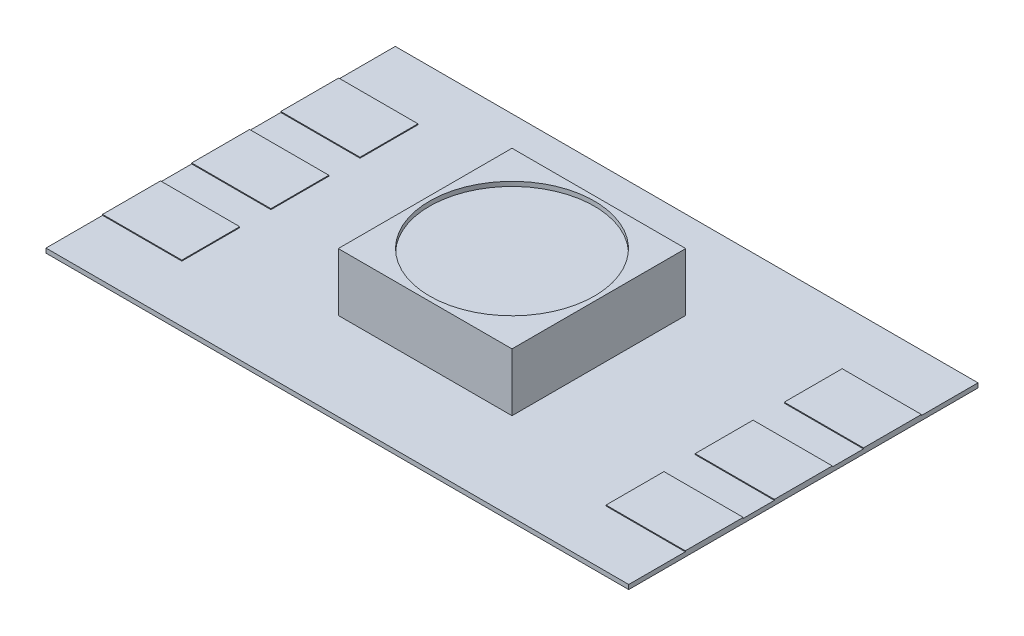
SolidWorks part; units mm, degrees
ref_plane "Front Plane" through (0, 0, 0) normal (0, 0, 1) x (1, 0, 0)
ref_plane "Top Plane" through (0, 0, 0) normal (0, 1, 0) x (1, 0, 0)
ref_plane "Right Plane" through (0, 0, 0) normal (1, 0, 0) x (0, 0, -1)
sketch "Sketch1" plane through (0, 0, 0) normal (0, 1, 0) x (1, 0, 0)
  line L0 (-8.3058, 4.9784) -> (8.3058, -4.9784) construction
  line L1 (-8.3058, 4.9784) -> (8.3058, 4.9784)
  line L2 (-8.3058, 4.9784) -> (-8.3058, -4.9784)
  line L3 (-8.3058, -4.9784) -> (8.3058, -4.9784)
  line L4 (8.3058, 4.9784) -> (8.3058, -4.9784)
  dimension "D1" = 9.9568
  dimension "D2" = 16.6116
extrude "Boss-Extrude1" add sketch "Sketch1" along normal blind 0.127
sketch "Sketch3" plane through (0, 0.127, 0) normal (0, 1, 0) x (1, 0, 0)
  line L0 (-8.3058, 4.9784) -> (8.3058, -4.9784) construction
  line L1 (-2.4765, 2.4765) -> (2.4765, -2.4765) construction
  line L2 (-2.4765, 2.4765) -> (2.4765, 2.4765)
  line L3 (-2.4765, 2.4765) -> (-2.4765, -2.4765)
  line L4 (-2.4765, -2.4765) -> (2.4765, -2.4765)
  line L5 (2.4765, 2.4765) -> (2.4765, -2.4765)
  dimension "D1" = 4.953
extrude "Boss-Extrude3" add sketch "Sketch3" along normal blind 1.651
sketch "Sketch4" plane through (0, 0.127, 0) normal (0, 1, 0) x (1, 0, 0)
  line L0 (-8.3058, 0) -> (8.3058, 0) construction
  line L1 (-8.3058, 4.9784) -> (-8.3058, -4.9784) construction
  line L2 (8.3058, -4.9784) -> (8.3058, 4.9784) construction
  line L3 (-6.047, 0) -> (-8.3058, 0) construction
  line L4 (-8.3058, 0.8255) -> (-6.047, 0.8255)
  line L5 (-8.3058, 0.8255) -> (-8.3058, -0.8255)
  line L6 (-8.3058, -0.8255) -> (-6.047, -0.8255)
  line L7 (-6.047, 0.8255) -> (-6.047, -0.8255)
  line L8 (-8.3058, 3.3655) -> (-6.047, 3.3655)
  line L9 (-6.047, 3.3655) -> (-6.047, 1.7145)
  line L10 (-8.3058, 1.7145) -> (-6.047, 1.7145)
  line L11 (-8.3058, 3.3655) -> (-8.3058, 1.7145)
  line L12 (-6.047, -3.3655) -> (-6.047, -1.7145)
  line L13 (-8.3058, -1.7145) -> (-6.047, -1.7145)
  line L14 (-8.3058, -3.3655) -> (-8.3058, -1.7145)
  line L15 (-8.3058, -3.3655) -> (-6.047, -3.3655)
  line L16 (0, 0) -> (0, -4.9784) construction
  line L17 (-8.3058, -4.9784) -> (8.3058, -4.9784) construction
  line L18 (8.3058, -3.3655) -> (8.3058, -1.7145)
  line L19 (8.3058, -3.3655) -> (6.047, -3.3655)
  line L20 (6.047, -3.3655) -> (6.047, -1.7145)
  line L21 (8.3058, -1.7145) -> (6.047, -1.7145)
  line L22 (8.3058, 0.8255) -> (8.3058, -0.8255)
  line L23 (8.3058, -0.8255) -> (6.047, -0.8255)
  line L24 (6.047, 0.8255) -> (6.047, -0.8255)
  line L25 (8.3058, 0.8255) -> (6.047, 0.8255)
  line L26 (8.3058, 1.7145) -> (6.047, 1.7145)
  line L27 (6.047, 3.3655) -> (6.047, 1.7145)
  line L28 (8.3058, 3.3655) -> (8.3058, 1.7145)
  line L29 (8.3058, 3.3655) -> (6.047, 3.3655)
  dimension "D1" = 1.651
  dimension "D2" = 2
extrude "Boss-Extrude4" add sketch "Sketch4" along normal blind 0.0254
sketch "Sketch5" plane through (0, 1.778, 0) normal (0, 1, 0) x (1, 0, 0)
  circle A0 centre (0, 0) radius 2.3483
extrude "Cut-Extrude1" cut sketch "Sketch5" against normal blind 0.127
pattern_linear "LPattern1" [suppressed] count 4 spacing 16.6116
